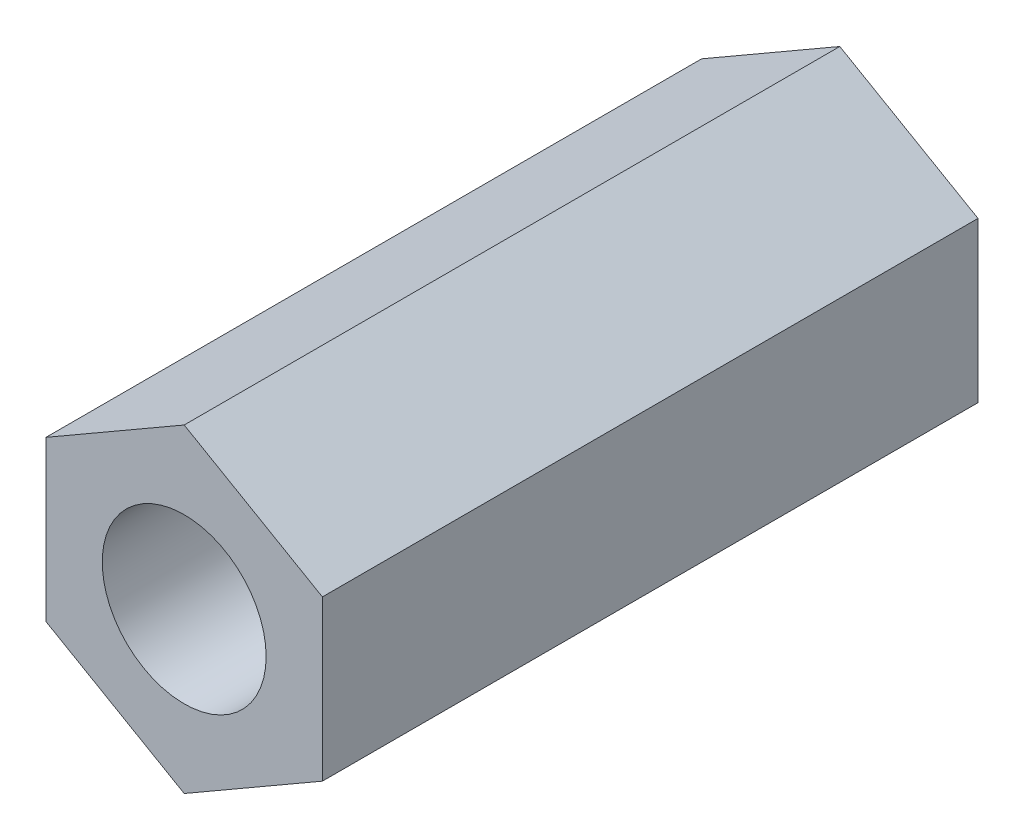
SolidWorks part; units mm, degrees
ref_plane "Front Plane" through (0, 0, 0) normal (0, 0, 1) x (1, 0, 0)
ref_plane "Top Plane" through (0, 0, 0) normal (0, 1, 0) x (1, 0, 0)
ref_plane "Right Plane" through (0, 0, 0) normal (1, 0, 0) x (0, 0, -1)
sketch "Sketch1" plane through (0, 0, 0) normal (0, 0, 1) x (1, 0, 0)
  line L1 (-62.8016, 33.5382) -> (-60.4457, 34.8983)
  line L2 (-60.4457, 34.8983) -> (-60.4457, 37.6187)
  line L3 (-60.4457, 37.6187) -> (-62.8016, 38.9788)
  line L4 (-62.8016, 38.9788) -> (-65.1574, 37.6187)
  line L5 (-65.1574, 37.6187) -> (-65.1574, 34.8983)
  line L6 (-65.1574, 34.8983) -> (-62.8016, 33.5382)
  circle A0 centre (-62.8016, 36.2585) radius 1.397 construction
  circle A1 centre (-62.8016, 36.2585) radius 1.397
  circle A2 centre (-62.8016, 36.2585) radius 2.3558 construction
  dimension "D1" = 4.7117
extrude "Boss-Extrude1" add sketch "Sketch1" along normal blind 11.176
